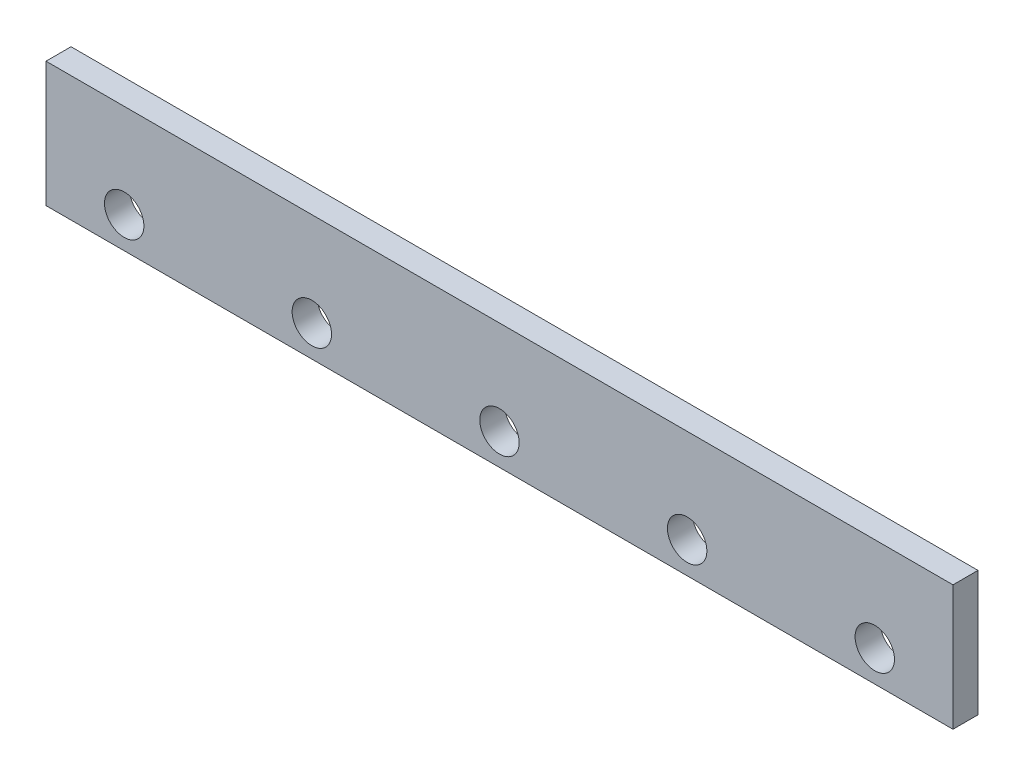
SolidWorks part; units mm, degrees
ref_plane "Front Plane" through (0, 0, 0) normal (0, 0, 1) x (1, 0, 0)
ref_plane "Top Plane" through (0, 0, 0) normal (0, 1, 0) x (1, 0, 0)
ref_plane "Right Plane" through (0, 0, 0) normal (1, 0, 0) x (0, 0, -1)
sketch "Sketch1" plane through (0, 0, 0) normal (0, 0, 1) x (1, 0, 0)
  line L1 (0, 0) -> (580, 0)
  line L2 (0, 0) -> (0, 80)
  line L3 (0, 80) -> (580, 80)
  line L4 (580, 0) -> (580, 80)
  dimension "D1" = 580
  dimension "D2" = 80
extrude "Boss-Extrude1" add sketch "Sketch1" along normal blind 16
sketch "Sketch2" plane through (0, 0, 0) normal (0, 0, 1) x (1, 0, 0)
  line L0 (0, 80) -> (0, 0) construction
  line L1 (0, 0) -> (580, 0) construction
  circle A0 centre (50, 20) radius 12.6
  circle A1 centre (170, 20) radius 12.6
  circle A2 centre (290, 20) radius 12.6
  circle A3 centre (410, 20) radius 12.6
  circle A4 centre (530, 20) radius 12.6
  dimension "D1" = 25.2
  dimension "D4" = 25.2
  dimension "D8" = 25.2
  dimension "D2" = 50
  dimension "D3" = 20
  dimension "D5" = 120
  dimension "D6" = 120
  dimension "D7" = 120
  dimension "D9" = 120
extrude "Cut-Extrude7" cut sketch "Sketch2" along normal blind 16
